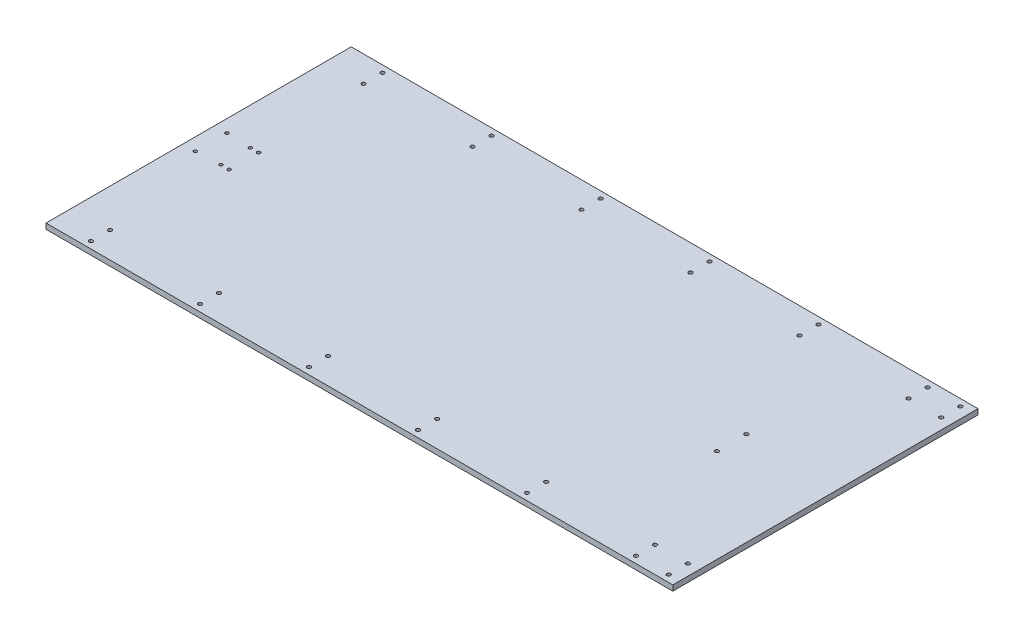
SolidWorks part; units mm, degrees
ref_plane "Спереди" through (0, 0, 0) normal (0, 0, 1) x (1, 0, 0)
ref_plane "Сверху" through (0, 0, 0) normal (0, 1, 0) x (1, 0, 0)
ref_plane "Справа" through (0, 0, 0) normal (1, 0, 0) x (0, 0, -1)
sketch "Эскиз1" plane through (0, 0, 0) normal (0, 1, 0) x (1, 0, 0)
  line L0 (-276.7974, 6.2908) -> (-314.5425, 6.2908) construction
  line L1 (-276.7974, 286.2908) -> (873.2026, 286.2908)
  line L2 (-276.7974, 286.2908) -> (-276.7974, -273.7092)
  line L3 (-276.7974, -273.7092) -> (873.2026, -273.7092)
  line L4 (873.2026, 286.2908) -> (873.2026, -273.7092)
  line L5 (223.2026, 187.065) -> (223.2026, 256.4984) construction
  line L6 (-208.7974, 33.2908) -> (-193.7974, 33.2908) construction
  line L7 (-263.8434, 256.2908) -> (-206.7974, 256.2908) construction
  line L8 (-206.7974, 273.7908) -> (-6.7974, 273.7908) construction
  line L9 (793.2026, 273.7908) -> (853.2026, 273.7908) construction
  circle A0 centre (-253.7974, 35.2908) radius 3
  circle A1 centre (-208.7974, 33.2908) radius 3
  circle A2 centre (-193.7974, 33.2908) radius 3
  circle A3 centre (-206.7974, 273.7908) radius 3.5
  circle A4 centre (-6.7974, 273.7908) radius 3.5
  circle A5 centre (193.2026, 273.7908) radius 3.5
  circle A6 centre (393.2026, 273.7908) radius 3.5
  circle A7 centre (593.2026, 273.7908) radius 3.5
  circle A10 centre (593.2026, 238.7908) radius 3.5
  circle A11 centre (393.2026, 238.7908) radius 3.5
  circle A12 centre (193.2026, 238.7908) radius 3.5
  circle A13 centre (-6.7974, 238.7908) radius 3.5
  circle A14 centre (-206.7974, 238.7908) radius 3.5
  circle A15 centre (593.2026, -226.2092) radius 3.5
  circle A18 centre (593.2026, -261.2092) radius 3.5
  circle A19 centre (393.2026, -226.2092) radius 3.5
  circle A20 centre (393.2026, -261.2092) radius 3.5
  circle A21 centre (193.2026, -226.2092) radius 3.5
  circle A22 centre (193.2026, -261.2092) radius 3.5
  circle A23 centre (-6.7974, -226.2092) radius 3.5
  circle A24 centre (-6.7974, -261.2092) radius 3.5
  circle A25 centre (-206.7974, -226.2092) radius 3.5
  circle A26 centre (-206.7974, -261.2092) radius 3.5
  circle A27 centre (701.2026, 33.2908) radius 3.5
  circle A28 centre (701.2026, -20.7092) radius 3.5
  circle A29 centre (-193.7974, -20.7092) radius 3
  circle A30 centre (-208.7974, -20.7092) radius 3
  circle A31 centre (-253.7974, -22.7092) radius 3
  circle A32 centre (793.2026, 273.7908) radius 3.5
  circle A33 centre (793.2026, 238.7908) radius 3.5
  circle A34 centre (793.2026, -226.2092) radius 3.5
  circle A35 centre (793.2026, -261.2092) radius 3.5
  circle A36 centre (853.2026, 273.7908) radius 3.5
  circle A37 centre (853.2026, 238.7908) radius 3.5
  circle A38 centre (853.2026, -226.2092) radius 3.5
  circle A39 centre (853.2026, -261.2092) radius 3.5
  dimension "D3" = 6
  dimension "D10" = 7
  dimension "D18" = 7
  dimension "D1" = 280
  dimension "D2" = 280
  dimension "D4" = 23
  dimension "D5" = 29
  dimension "D7" = 2
  dimension "D9" = 15
  dimension "D11" = 12.5
  dimension "D12" = 70
  dimension "D13" = 17.5
  dimension "D15" = 200
  dimension "D16" = 60
  dimension "D19" = 27
  dimension "D32" = 978
  dimension "D6" = 1150
  dimension "D8" = 2
  dimension "D14" = 6
extrude "Бобышка-Вытянуть1" add sketch "Эскиз1" along normal blind 10
